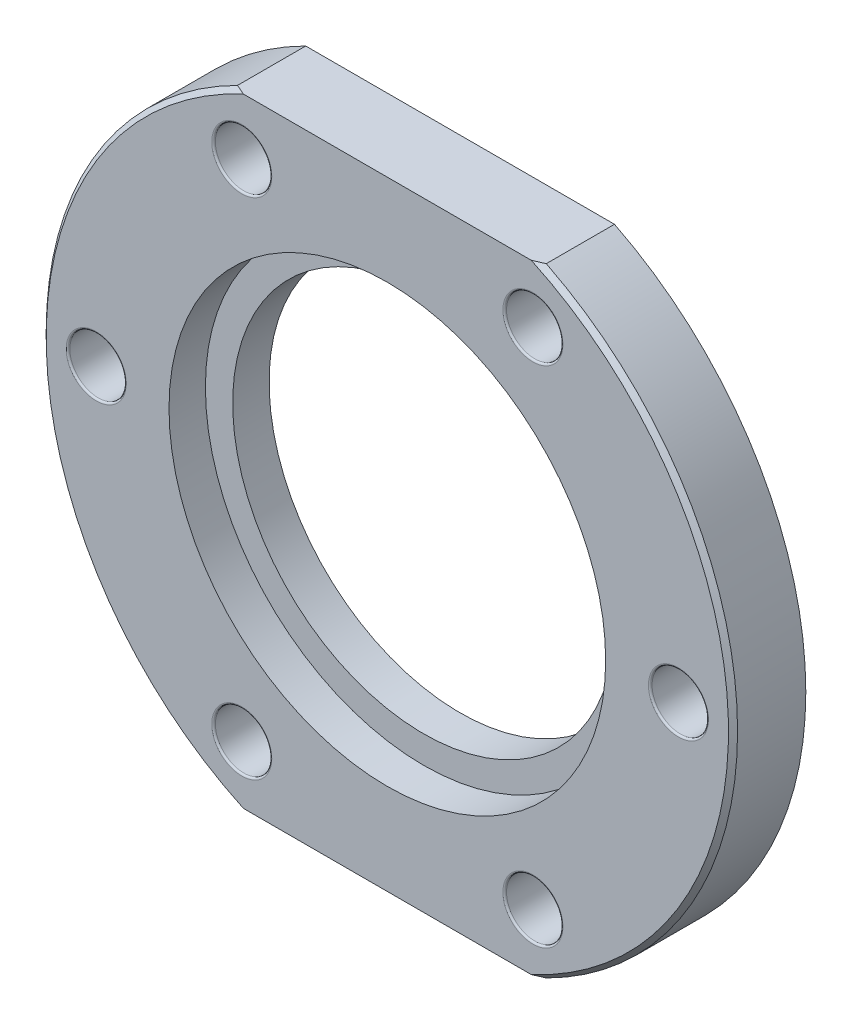
SolidWorks part; units mm, degrees
material "Stainless Steel (ferritic)"
ref_plane "Front Plane" through (0, 0, 0) normal (0, 0, 1) x (1, 0, 0)
ref_plane "Top Plane" through (0, 0, 0) normal (0, 1, 0) x (1, 0, 0)
ref_plane "Right Plane" through (0, 0, 0) normal (1, 0, 0) x (0, 0, -1)
sketch "Sketch1" plane through (0, 0, 0) normal (0, 0, 1) x (1, 0, 0)
  circle A0 centre (0, 0) radius 19
  dimension "D1" = 38
extrude "Boss-Extrude1" add sketch "Sketch1" along normal blind 4
sketch "Sketch2" plane through (0, 0, 4) normal (0, 0, 1) x (1, 0, 0)
  line L0 (-18.9383, 17) -> (18.9383, 17)
  line L1 (-27.797, 0) -> (27.797, 0)
  line L2 (-18.9383, -17) -> (18.9383, -17)
  arc A0 (-18.9383, 17) -> (18.9383, 17) centre (0, -71.665) cw
  arc A1 (18.9383, -17) -> (-18.9383, -17) centre (0, 55.454) cw
  point P6 (0, 0)
  circle M6 centre (0, 0) radius 19
  dimension "D1" = 17
extrude "Cut-Extrude1" cut sketch "Sketch2" against normal through all both and the other way through all contours L2 M6 | L0 M6
sketch "Sketch3" plane through (0, 0, 4) normal (0, 0, 1) x (1, 0, 0)
  circle A0 centre (0, 0) radius 16 construction
  circle A7 centre (-16, 0) radius 1.55
  circle A8 centre (-8, 13.8564) radius 1.55
  circle A9 centre (8, 13.8564) radius 1.55
  circle A10 centre (16, 0) radius 1.55
  circle A11 centre (8, -13.8564) radius 1.55
  circle A12 centre (-8, -13.8564) radius 1.55
  point P17 (0, 0)
  point P18 (-0.8814, 0)
  dimension "D1" = 32
  dimension "D2" = 3.1
  dimension "D3" = 6
extrude "Cut-Extrude2" cut sketch "Sketch3" against normal through all both and the other way through all
fillet "Fillet1" radius 0.1 12 edges at (17.55, 0, 0) (17.55, 0, 4) (9.55, -13.8564, 0) (9.55, -13.8564, 4) (-6.45, -13.8564, 0) (-6.45, -13.8564, 4) (-14.45, 0, 0) (-14.45, 0, 4) (9.55, 13.8564, 0) (9.55, 13.8564, 4) (-6.45, 13.8564, 0) (-6.45, 13.8564, 4)
sketch "Sketch4" plane through (0, 0, 4) normal (0, 0, 1) x (1, 0, 0)
  circle A0 centre (0, 0) radius 12
  dimension "D1" = 24
extrude "Cut-Extrude3" cut sketch "Sketch4" against normal blind 2 and the other way through all
sketch "Sketch5" plane through (0, 0, 2) normal (0, 0, 1) x (1, 0, 0)
  circle A0 centre (0, 0) radius 10.5
  dimension "D1" = 21
extrude "Cut-Extrude4" cut sketch "Sketch5" against normal blind 2
chamfer "Chamfer2" distance 0.25 angle 45 2 edges at (-19, 0, 4) (19, 0, 4)
